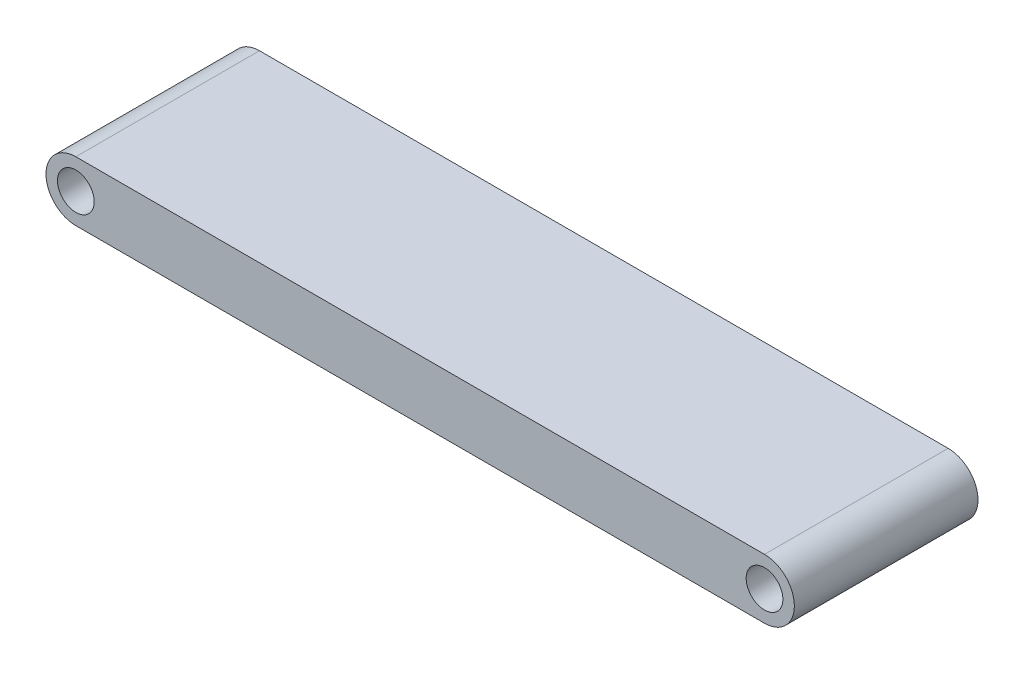
SolidWorks part; units mm, degrees
ref_plane "Płaszczyzna przednia" through (0, 0, 0) normal (0, 0, 1) x (1, 0, 0)
ref_plane "Płaszczyzna górna" through (0, 0, 0) normal (0, 1, 0) x (1, 0, 0)
ref_plane "Płaszczyzna prawa" through (0, 0, 0) normal (1, 0, 0) x (0, 0, -1)
sketch "Szkic1" plane through (0, 0, 0) normal (0, 0, 1) x (1, 0, 0)
  line L0 (-3.3553, 6.5) -> (146.6447, 6.5)
  line L1 (-3.3553, -6.5) -> (146.6447, -6.5)
  circle A0 centre (-3.3553, 0) radius 4
  arc A1 (-3.3553, 6.5) -> (-3.3553, -6.5) centre (-3.3553, 0) ccw
  circle A2 centre (146.6447, 0) radius 4
  arc A3 (146.6447, -6.5) -> (146.6447, 6.5) centre (146.6447, 0) ccw
  dimension "D1" = 150
  dimension "D2" = 8
  dimension "D3" = 6.5
  dimension "D4" = 6.5
  dimension "D5" = 8
extrude "Dodanie-wyciągnięcie1" add sketch "Szkic1" along normal blind 40
